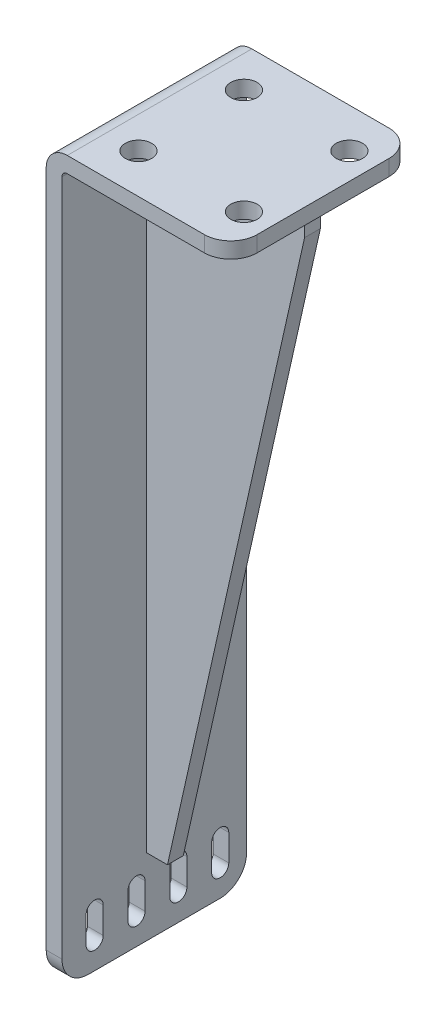
SolidWorks part; units mm, degrees
material "普通碳钢"
ref_plane "前视基准面" through (0, 0, 0) normal (0, 0, 1) x (1, 0, 0)
ref_plane "上视基准面" through (0, 0, 0) normal (0, 1, 0) x (1, 0, 0)
ref_plane "右视基准面" through (0, 0, 0) normal (1, 0, 0) x (0, 0, -1)
sketch "草图1" plane through (0, 0, 0) normal (0, 0, 1) x (1, 0, 0)
  line L0 (8, 0) -> (70, 0)
  line L1 (70, 0) -> (70, -6)
  line L2 (70, -6) -> (8, -6)
  line L3 (6, -8) -> (6, -275)
  line L4 (6, -275) -> (0, -275)
  line L5 (0, -275) -> (0, -8)
  arc A0 (8, 0) -> (0, -8) centre (8, -8) ccw
  arc A1 (8, -6) -> (6, -8) centre (8, -8) ccw
  point P9 (0, 0)
  dimension "D5" = 8
  dimension "D6" = 2
  dimension "D1" = 6
  dimension "D2" = 6
  dimension "D3" = 275
  dimension "D4" = 70
extrude "凸台-拉伸1" add sketch "草图1" along normal blind 70
fillet "圆角1" radius 10 4 edges at (3, -275, 0) (3, -275, 70) (70, -3, 0) (70, -3, 70)
sketch "草图2" plane through (0, 0, 0) normal (-1, 0, 0) x (0, 0, 1)
  line L0 (0, -265) -> (70, -265) construction
  line L1 (0, -8) -> (0, -265) construction
  line L2 (70, -8) -> (70, -265) construction
  line L3 (60, -275) -> (10, -275) construction
  line L4 (6.75, -255) -> (6.75, -265)
  line L5 (13.25, -255) -> (13.25, -265)
  line L6 (22.625, -255) -> (22.625, -265)
  line L7 (38.5, -255) -> (38.5, -265)
  line L8 (29.125, -265) -> (29.125, -255)
  line L9 (45, -255) -> (45, -265)
  line L10 (54.375, -255) -> (54.375, -265)
  line L11 (60.875, -255) -> (60.875, -265)
  arc A0 (6.75, -265) -> (13.25, -265) centre (10, -265) ccw
  arc A1 (22.625, -265) -> (29.125, -265) centre (25.875, -265) ccw
  arc A2 (38.5, -265) -> (45, -265) centre (41.75, -265) ccw
  arc A3 (54.375, -265) -> (60.875, -265) centre (57.625, -265) ccw
  arc A6 (13.25, -255) -> (6.75, -255) centre (10, -255) ccw
  arc A7 (29.125, -255) -> (22.625, -255) centre (25.875, -255) ccw
  arc A8 (45, -255) -> (38.5, -255) centre (41.75, -255) ccw
  arc A9 (60.875, -255) -> (54.375, -255) centre (57.625, -255) ccw
  dimension "D2" = 6.5
  dimension "D4" = 15.875
  dimension "D6" = 2
  dimension "D1" = 10
  dimension "D5" = 10
  dimension "D7" = 10
  dimension "D3" = 4
extrude "切除-拉伸1" cut sketch "草图2" against normal up to next
sketch "草图3" plane through (0, 0, 0) normal (0, 1, 0) x (1, 0, 0)
  line L0 (60, 0) -> (8, 0) construction
  line L2 (8, -70) -> (8, 0) construction
  line L3 (8, -35) -> (9.6268, -36.9767) construction
  line L4 (60, -15) -> (20, -15) construction
  line L5 (60, -15) -> (60, -55) construction
  line L6 (60, -55) -> (20, -55) construction
  line L7 (20, -15) -> (20, -55) construction
  line L8 (70, -60) -> (70, -10) construction
  circle A0 centre (60, -15) radius 5
  circle A1 centre (20, -15) radius 5
  circle A2 centre (20, -55) radius 5
  circle A3 centre (60, -55) radius 5
  dimension "D5" = 10
  dimension "D1" = 40
  dimension "D2" = 40
  dimension "D3" = 15
  dimension "D4" = 10
extrude "切除-拉伸2" cut sketch "草图3" against normal up to next
ref_plane "基准面1" through (0, 0, 35) normal (0, 0, -1) x (-1, 0, 0)
sketch "草图4" plane through (0, 0, 35) normal (0, 0, -1) x (-1, 0, 0)
  line L0 (-6, -14) -> (-6, -246)
  line L1 (-6, -265) -> (-6, -8) construction
  line L2 (-6, -246) -> (-14, -246)
  line L3 (-14, -246) -> (-66, -14)
  line L4 (-66, -14) -> (-66, -6)
  line L5 (-66, -6) -> (-14, -6)
  line L6 (-14, -6) -> (-6, -14)
  line L7 (-8, -6) -> (-60, -6) construction
  dimension "D1" = 8
  dimension "D2" = 8
  dimension "D3" = 240
  dimension "D4" = 60
  dimension "D5" = 8
  dimension "D6" = 8
extrude "凸台-拉伸2" add sketch "草图4" along normal mid plane 6
